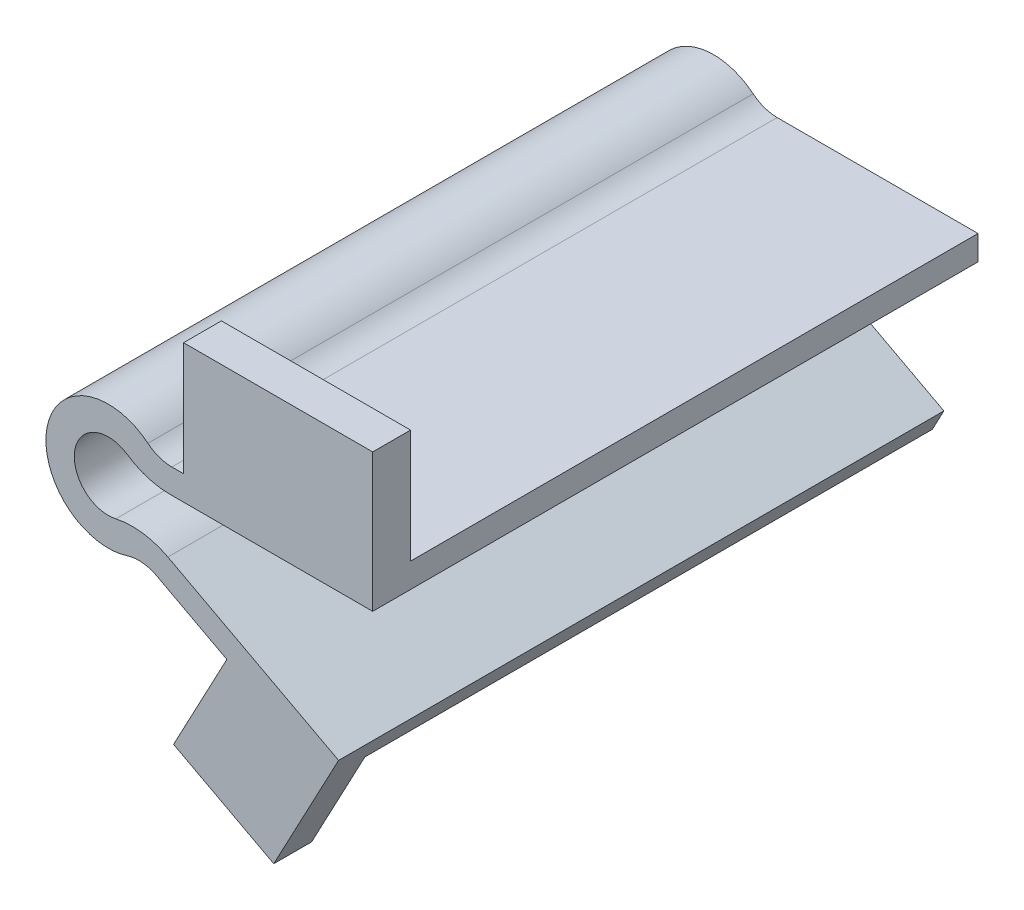
SolidWorks part; units mm, degrees
ref_plane "Front Plane" through (0, 0, 0) normal (0, 0, 1) x (1, 0, 0)
ref_plane "Top Plane" through (0, 0, 0) normal (0, 1, 0) x (1, 0, 0)
ref_plane "Right Plane" through (0, 0, 0) normal (1, 0, 0) x (0, 0, -1)
sketch "Sketch5" plane through (4.2285, 0, 0) normal (0, 0, 1) x (1, 0, 0)
  line L1 (2.7601, 0.4) -> (-3.4223, 0.4)
  line L3 (-2.9557, 1.05) -> (2.7601, 1.05)
  line L4 (2.7601, 0.4) -> (2.7601, 1.05)
  line L5 (2.7601, 1.05) -> (-2.9557, 1.05)
  line L8 (1.8583, -3.4629) -> (-3.5476, -0.5885)
  line L10 (3.7715, 0) -> (12.1311, 0) construction
  line L12 (-4.2285, 0) -> (3.1715, 0) construction
  line L20 (1.8583, -3.4629) -> (1.5531, -4.0368)
  line L21 (-3.3789, -1.4144) -> (1.5531, -4.0368)
  line L22 (-4.2285, 0) -> (1.9522, -3.2863) construction
  arc A1 (-2.9557, 1.05) -> (-3.3789, -1.4144) centre (-4.2285, 0) ccw
  arc A2 (-3.4223, 0.4) -> (-3.5476, -0.5885) centre (-4.2285, 0) ccw
  circle A3 centre (-4.2285, 0) radius 7 construction
  dimension "D6" = 0.75
  dimension "D8" = 0.9
  dimension "D2" = 14
  dimension "D3" = 0.65
  dimension "D7" = 0.65
  dimension "D9" = 28
  dimension "D12" = 0.4
  dimension "D13" = 0.2
extrude "Boss-Extrude2" add sketch "Sketch5" along normal blind 16 separate body
fillet "Fillet3" radius 1 2 edges at (1.2728, 1.05, 8) (0.8496, -1.4144, 8)
fillet "Fillet6" radius 2 2 edges at (0.6809, -0.5885, 8) (0.8062, 0.4, 8)
sketch "Sketch7" plane through (0, 0, 16) normal (0, 0, 1) x (1, 0, 0)
  line L0 (6.9886, 4.05) -> (1.9886, 4.05)
  line L1 (6.9886, 1.05) -> (1.9886, 1.05)
  line L2 (6.9886, 1.05) -> (6.9886, 4.05)
  line L5 (1.6793, 1.05) -> (6.9886, 1.05) construction
  line L8 (1.9886, 4.05) -> (1.9886, 1.05)
  line L9 (5.7816, -4.0368) -> (4.3732, -6.6856)
  line L10 (4.3732, -6.6856) -> (1.7243, -5.2772)
  line L11 (1.7243, -5.2772) -> (3.1327, -2.6284)
  line L12 (1.2762, -1.6413) -> (5.7816, -4.0368) construction
  line L13 (6.0867, -3.4629) -> (5.7816, -4.0368) construction
  line L16 (3.1327, -2.6284) -> (5.7816, -4.0368)
  dimension "D1" = 3
  dimension "D2" = 5
  dimension "D3" = 3
extrude "Boss-Extrude6" add sketch "Sketch7" against normal blind 1
